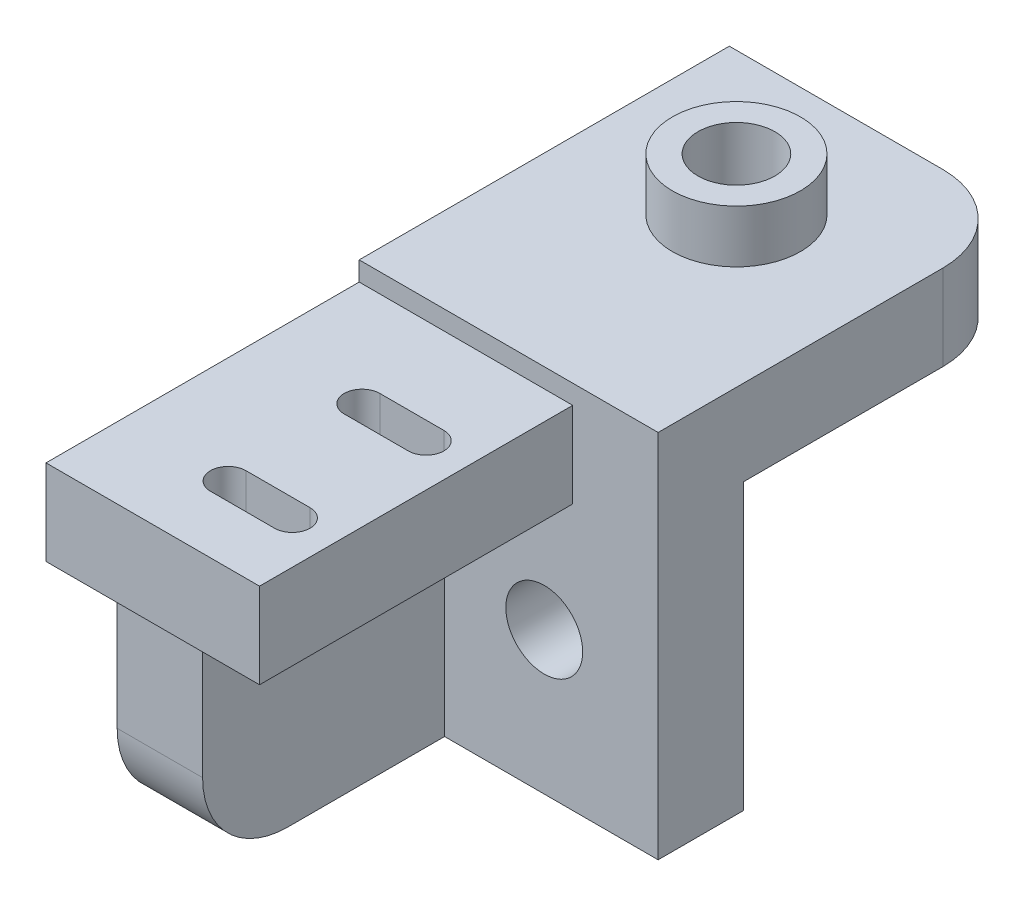
SolidWorks part; units mm, degrees
ref_plane "Płaszczyzna przednia" through (0, 0, 0) normal (0, 0, 1) x (1, 0, 0)
ref_plane "Płaszczyzna górna" through (0, 0, 0) normal (0, 1, 0) x (1, 0, 0)
ref_plane "Płaszczyzna prawa" through (0, 0, 0) normal (1, 0, 0) x (0, 0, -1)
sketch "Szkic1" plane through (0, 0, 0) normal (0, 0, 1) x (1, 0, 0)
  line L1 (0, 0) -> (21, 0)
  line L2 (0, 0) -> (0, 20)
  line L3 (0, 20) -> (21, 20)
  line L4 (21, 0) -> (21, 20)
  line L5 (0, 20) -> (21, 20)
  line L6 (0, 20) -> (0, 26)
  line L7 (0, 26) -> (21, 26)
  line L8 (21, 20) -> (21, 26)
  circle A0 centre (13, 10) radius 2.7
  dimension "D3" = 5.4
  dimension "D1" = 20
  dimension "D2" = 21
  dimension "D4" = 10
  dimension "D5" = 8
  dimension "D6" = 6
extrude "Dodanie-wyciągnięcie1" add sketch "Szkic1" along normal blind 6 contours L3 L8 L7 L6 | L1 L4 L3 L2 A0
sketch "Szkic2" plane through (0, 0, 0) normal (0, 0, -1) x (-1, 0, 0)
  line L0 (0, 0) -> (0, 26) construction
  line L1 (-21, 26) -> (0, 26)
  line L2 (-21, 26) -> (-21, 20)
  line L3 (-21, 20) -> (0, 20)
  line L4 (0, 26) -> (0, 20)
  dimension "D1" = 6
extrude "Dodanie-wyciągnięcie2" add sketch "Szkic2" along normal blind 20
sketch "Szkic3" plane through (0, 26, 0) normal (0, 1, 0) x (1, 0, 0)
  line L0 (0, -6) -> (0, 20) construction
  line L2 (0, 20) -> (21, 20) construction
  circle A0 centre (10.5, 10) radius 2.7
  dimension "D3" = 5.4
  dimension "D1" = 10.5
  dimension "D2" = 10
extrude "Wytnij-wyciągnięcie1" cut sketch "Szkic3" against normal blind 9
sketch "Szkic4" plane through (0, 0, 6) normal (0, 0, 1) x (1, 0, 0)
  line L0 (0, 0) -> (0, 26) construction
  line L1 (0, 18.65) -> (15, 18.65)
  line L2 (0, 18.65) -> (0, 24.65)
  line L3 (0, 24.65) -> (15, 24.65)
  line L6 (15, 24.65) -> (15, 18.65)
  dimension "D1" = 24.65
  dimension "D2" = 6
  dimension "D3" = 15
extrude "Dodanie-wyciągnięcie3" add sketch "Szkic4" along normal blind 22
sketch "Szkic8" plane through (0, 26, 0) normal (0, 1, 0) x (1, 0, 0)
  circle A0 centre (10.5, 10) radius 2.7
  circle A1 centre (10.5, 10) radius 4.5
  dimension "D1" = 9
  dimension "D2" = 5.4
extrude "Dodanie-wyciągnięcie6" add sketch "Szkic8" along normal blind 3.7
sketch "Szkic9" plane through (0, 0, 6) normal (0, 0, 1) x (1, 0, 0)
  line L0 (0, 18.65) -> (15, 18.65) construction
  line L1 (0, 0) -> (6, 0)
  line L2 (0, 0) -> (0, 18.65)
  line L3 (0, 18.65) -> (6, 18.65)
  line L4 (6, 0) -> (6, 18.65)
  dimension "D1" = 6
extrude "Dodanie-wyciągnięcie7" add sketch "Szkic9" along normal blind 17
fillet "Zaokrąglenie3" radius 6 1 edges at (3, 0, 23)
sketch "Szkic12" plane through (0, 24.65, 0) normal (0, 1, 0) x (1, 0, 0)
  line L0 (12, -13.3) -> (7.5, -13.3) construction
  line L1 (12, -14.55) -> (7.5, -14.55)
  line L2 (12, -12.05) -> (7.5, -12.05)
  line L3 (15, -28) -> (15, -6) construction
  line L5 (15, -18) -> (0, -18) construction
  line L6 (0, -28) -> (0, -6) construction
  line L7 (12, -22.7) -> (7.5, -22.7) construction
  line L8 (12, -21.45) -> (7.5, -21.45)
  line L9 (12, -23.95) -> (7.5, -23.95)
  arc A0 (12, -14.55) -> (12, -12.05) centre (12, -13.3) ccw
  arc A1 (7.5, -12.05) -> (7.5, -14.55) centre (7.5, -13.3) ccw
  arc A2 (12, -21.45) -> (12, -23.95) centre (12, -22.7) cw
  arc A3 (7.5, -23.95) -> (7.5, -21.45) centre (7.5, -22.7) cw
  point P2 (9.75, -13.3)
  point P16 (9.75, -22.7)
  dimension "D1" = 1.25
  dimension "D2" = 4.5
  dimension "D3" = 3
  dimension "D4" = 6.05
  dimension "D5" = 3.45
extrude "Wytnij-wyciągnięcie2" cut sketch "Szkic12" against normal blind 22
fillet "Zaokrąglenie4" radius 6 1 edges at (21, 23, -20)
sketch "Szkic6" plane through (0, 26, 0) normal (0, 1, 0) x (1, 0, 0)
  circle A0 centre (10.5, 10) radius 2.7
  circle A1 centre (10.5, 10) radius 4.5
  dimension "D1" = 5.4
  dimension "D2" = 9
extrude "Dodanie-wyciągnięcie5" add sketch "Szkic6" along normal blind 3.7
